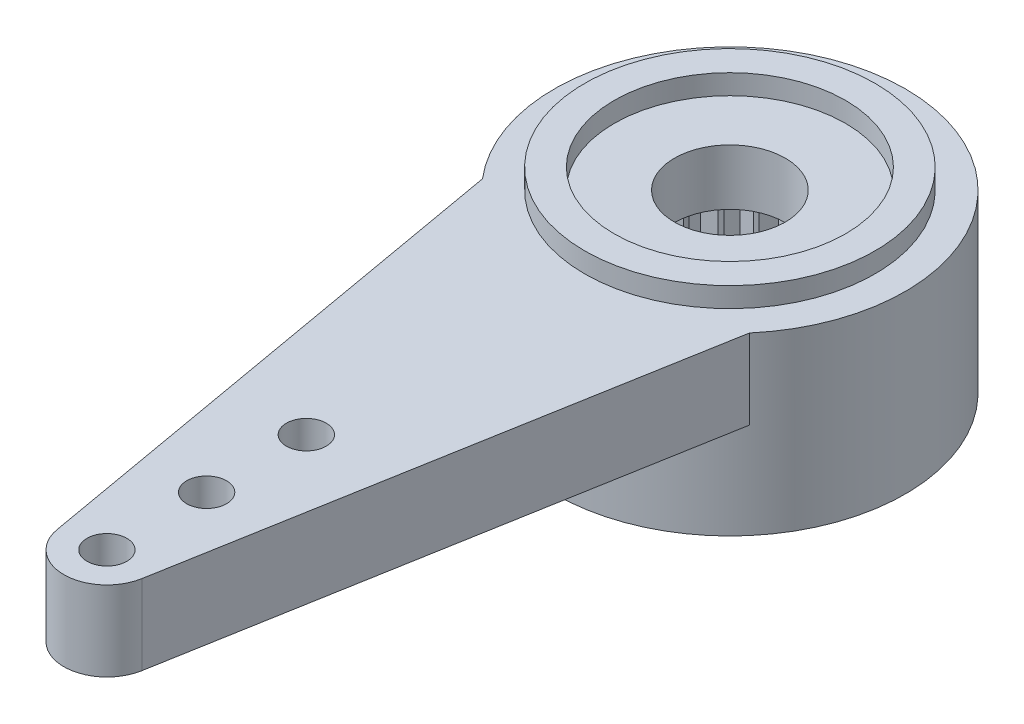
SolidWorks part; units mm, degrees
material "Polyethylene Cross-Linked"
ref_plane "Front Plane" through (0, 0, 0) normal (0, 0, 1) x (1, 0, 0)
ref_plane "Top Plane" through (0, 0, 0) normal (0, 1, 0) x (1, 0, 0)
ref_plane "Right Plane" through (0, 0, 0) normal (1, 0, 0) x (0, 0, -1)
sketch "Sketch1" plane through (0, 0, 0) normal (0, 1, 0) x (1, 0, 0)
  circle A0 centre (0, 0) radius 4.4
  dimension "D1" = 8.8
extrude "Boss-Extrude1" add sketch "Sketch1" along normal blind 4.4
sketch "Sketch2" plane through (0, 4.4, 0) normal (0, 1, 0) x (1, 0, 0)
  line L0 (0, 0) -> (0, 15.62) construction
  line L1 (-1.0636, 15.8075) -> (-3.3473, 2.8557)
  line L2 (0, 16.7) -> (0, 15.62) construction
  line L3 (1.0636, 15.8075) -> (3.3473, 2.8557)
  arc A0 (1.0636, 15.8075) -> (-1.0636, 15.8075) centre (0, 15.62) ccw
  arc A4 (3.3473, 2.8557) -> (-3.3473, 2.8557) centre (0, 0) ccw
  circle A5 centre (0, 0) radius 4.4 construction
  dimension "D1" = 2.16
  dimension "D2" = 16.7
  dimension "D3" = 10
extrude "Boss-Extrude2" add sketch "Sketch2" against normal blind 2
sketch "Sketch3" plane through (0, 4.4, 0) normal (0, -1, 0) x (-1, 0, 0)
  circle A0 centre (0, 0) radius 3.64
  circle A1 centre (0, 0) radius 2.9
  dimension "D1" = 7.28
  dimension "D2" = 5.8
extrude "Boss-Extrude3" add sketch "Sketch3" against normal blind 0.5
sketch "Sketch4" plane through (0, 4.4, 0) normal (0, -1, 0) x (-1, 0, 0)
  circle A0 centre (0, 0) radius 1.39
  dimension "D1" = 2.78
extrude "Cut-Extrude1" cut sketch "Sketch4" along normal through all
sketch "Sketch5" plane through (0, 0, 0) normal (0, -1, 0) x (-1, 0, 0)
  circle A0 centre (0, 15.62) radius 0.5
  dimension "D1" = 1
extrude "Cut-Extrude2" cut sketch "Sketch5" against normal through all
sketch "Sketch6" plane through (0, 0, 0) normal (0, 1, 0) x (1, 0, 0)
  line L0 (0, 0) -> (0, 15.62) construction
pattern_linear "LPattern1" count 3 spacing 2.5 along (0, 0, 1) of "Cut-Extrude2"
mirror "Mirror1" about plane through (0, 0, 0) normal (0, 0, 1) of "Boss-Extrude2", "LPattern1", "Cut-Extrude2"
sketch "Sketch7" plane through (0, 0, 0) normal (0, -1, 0) x (-1, 0, 0)
  line L0 (0.0508, -2.5995) -> (0.2907, -2.8854)
  line L1 (-0.0508, -2.5995) -> (-0.2907, -2.8854)
  line L2 (0, -2.6) -> (0, -2.9) construction
  line L3 (0, 0) -> (0.0508, -2.5995) construction
  line L4 (-0.0508, -2.5995) -> (0, 0) construction
  arc A0 (-0.2907, -2.8854) -> (0.2907, -2.8854) centre (0, 0) ccw
  arc A1 (-0.0508, -2.5995) -> (0.0508, -2.5995) centre (0, 0) ccw
  dimension "D1" = 5.8
  dimension "D2" = 5.2
  dimension "D3" = 80
  dimension "D4" = 2.24
sketch "Sketch8" plane through (0, 0, 0) normal (0, -1, 0) x (-1, 0, 0)
  line L0 (0, -2.9) -> (0.2629, -2.5867)
  line L1 (0, -2.9) -> (-0.2629, -2.5867)
  line L2 (0, -2.6) -> (0, -2.9) construction
  line L3 (0, 0) -> (0, -2.6) construction
  arc A1 (-0.2629, -2.5867) -> (0.2629, -2.5867) centre (0, 0) ccw
  dimension "D1" = 0.3
  dimension "D2" = 5.2
  dimension "D3" = 80
extrude "Cut-Extrude4" cut sketch "Sketch8" against normal blind 3
pattern_circular "CirPattern2" count 26 over 360 about axis through (0, 0, 0) along (0, 1, 0) of "Cut-Extrude4"
sketch "Sketch9" plane through (0, 0, 0) normal (0, -1, 0) x (-1, 0, 0)
  circle A0 centre (0, 0) radius 2.6
  arc A1 (-0.2629, -2.5867) -> (0.2629, -2.5867) centre (0, 0) ccw construction
extrude "Cut-Extrude5" cut sketch "Sketch9" against normal blind 3
sketch "Horn Trim Sketch" plane through (0, 0, 0) normal (0, -1, 0) x (1, 0, 0)
  line L2 (-4.4, 0) -> (-4.4, -16.7)
  line L3 (-4.4, -16.7) -> (4.4, -16.7)
  line L4 (4.4, 0) -> (4.4, -16.7)
  line L5 (0, 0) -> (4.4, -16.7) construction
  line L6 (-4.4, -16.7) -> (0, 0) construction
  circle A0 centre (0, 0) radius 4.4 construction
  arc A1 (-4.4, 0) -> (4.4, 0) centre (0, 0) ccw
  arc A2 (-1.0636, -15.8075) -> (1.0636, -15.8075) centre (0, -15.62) ccw construction
extrude "Cut-Extrude6" cut sketch "Horn Trim Sketch" against normal up to surface (4.9 mm away) up to face at (0, 4.9, -2.9)
